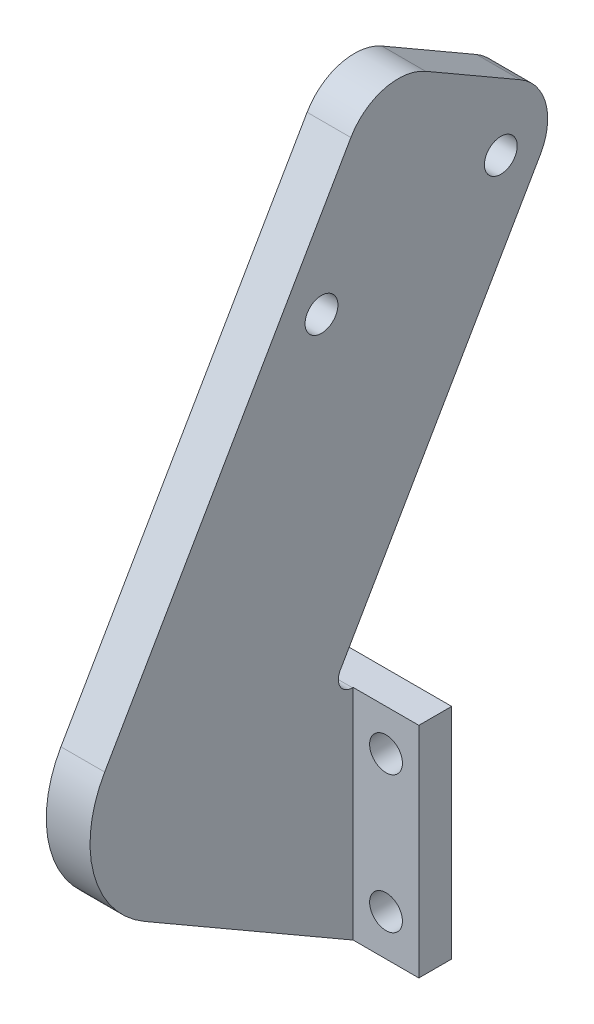
SolidWorks part; units mm, degrees
material "6061-T6 (SS)"
ref_plane "前视基准面" through (0, 0, 0) normal (0, 0, 1) x (1, 0, 0)
ref_plane "上视基准面" through (0, 0, 0) normal (0, 1, 0) x (1, 0, 0)
ref_plane "右视基准面" through (0, 0, 0) normal (1, 0, 0) x (0, 0, -1)
sketch "草图1" plane through (0, 0, 0) normal (0, 0, 1) x (1, 0, 0)
  line L1 (0, 0) -> (17, 0)
  line L2 (0, 0) -> (0, 20)
  line L3 (0, 20) -> (17, 20)
  line L4 (17, 0) -> (17, 20)
  circle A0 centre (3, 16.25) radius 1.5
  circle A1 centre (14, 16.25) radius 1.5
  circle A2 centre (14, 3.75) radius 1.5
  circle A3 centre (3, 3.75) radius 1.5
  dimension "D3" = 3
  dimension "D4" = 3.75
  dimension "D5" = 3
  dimension "D1" = 17
  dimension "D2" = 20
  dimension "D6" = 2
  dimension "D7" = 2
extrude "凸台-拉伸1" add sketch "草图1" along normal blind 3
ref_plane "基准面4" through (6, 0, 0) normal (-1, 0, 0) x (0, 0, 1)
sketch "草图3" plane through (6, 0, 0) normal (-1, 0, 0) x (0, 0, 1)
  line L0 (3, 20) -> (5.3094, 20)
  line L2 (0.7128, 67.9615) -> (30.7128, 16)
  line L3 (30.7128, 16) -> (3, 0)
  line L5 (3, 0) -> (0, 0) construction
  line L6 (3, 20) -> (3, 0) construction
  line L7 (3, 20) -> (3, 0)
  line L8 (5.3094, 20) -> (-16.6077, 57.9615)
  line L9 (-16.6077, 57.9615) -> (0.7128, 67.9615)
  dimension "D1" = 20
  dimension "D2" = 60
  dimension "D3" = 32
  dimension "D5" = 30
extrude "凸台-拉伸2" add sketch "草图3" against normal blind 5
sketch "草图4" plane through (11, 0, 0) normal (1, 0, 0) x (0, 0, -1)
  line L1 (-30.7128, 16) -> (-0.7128, 67.9615) construction
  line L3 (-0.7128, 67.9615) -> (16.6077, 57.9615) construction
  circle A0 centre (-5.8987, 50.9793) radius 1.5
  circle A1 centre (10.4936, 55.3716) radius 1.5
  dimension "D1" = 5.3
  dimension "D2" = 3
  dimension "D3" = 4
  dimension "D4" = 3
  dimension "D5" = 16.3923
  dimension "D6" = 16
extrude "切除-拉伸1" cut sketch "草图4" against normal blind 5
fillet "圆角2" radius 5 2 edges at (8.5, 67.9615, 0.7128) (8.5, 57.9615, -16.6077)
fillet "圆角3" radius 1.3 1 edges at (8.5, 20, 5.3094)
fillet "圆角4" radius 10 1 edges at (8.5, 16, 30.7128)
sketch "草图5" plane through (0, 0, 3) normal (0, 0, 1) x (1, 0, 0)
  line L1 (0, 20) -> (6, 20)
  line L2 (0, 20) -> (0, 0)
  line L3 (0, 0) -> (6, 0)
  line L4 (6, 20) -> (6, 0)
extrude "切除-拉伸2" cut sketch "草图5" against normal blind 10
sketch "草图6" plane through (6, 0, 0) normal (-1, 0, 0) x (0, 0, 1)
  line L7 (3, 0) -> (22.0526, 11)
  line L8 (25.7128, 24.6603) -> (3.2128, 63.6314)
  line L9 (-3.6173, 65.4615) -> (-12.2776, 60.4615)
  line L10 (-14.1077, 53.6314) -> (4.1836, 21.95)
  line L11 (3.0577, 20) -> (0, 20)
  line L12 (0, 20) -> (0, 0)
  line L13 (0, 0) -> (3, 0)
  line L14 (3, 0) -> (22.0526, 11)
  line L15 (25.7128, 24.6603) -> (3.2128, 63.6314)
  line L16 (-3.6173, 65.4615) -> (-12.2776, 60.4615)
  line L17 (-14.1077, 53.6314) -> (4.1836, 21.95)
  line L18 (3.0577, 20) -> (0, 20)
  line L19 (0, 20) -> (0, 0)
  line L20 (0, 0) -> (3, 0)
  circle A0 centre (5.8987, 50.9793) radius 1.5 construction
  circle A1 centre (-10.4936, 55.3716) radius 1.5 construction
  circle A2 centre (5.8987, 50.9793) radius 1.5
  circle A3 centre (-10.4936, 55.3716) radius 1.5
  arc A4 (22.0526, 11) -> (25.7128, 24.6603) centre (17.0526, 19.6603) ccw
  arc A5 (3.2128, 63.6314) -> (-3.6173, 65.4615) centre (-1.1173, 61.1314) ccw
  arc A6 (-12.2776, 60.4615) -> (-14.1077, 53.6314) centre (-9.7776, 56.1314) ccw
  arc A7 (3.0577, 20) -> (4.1836, 21.95) centre (3.0577, 21.3) ccw
  arc A8 (22.0526, 11) -> (25.7128, 24.6603) centre (17.0526, 19.6603) ccw
  arc A9 (3.2128, 63.6314) -> (-3.6173, 65.4615) centre (-1.1173, 61.1314) ccw
  arc A10 (-12.2776, 60.4615) -> (-14.1077, 53.6314) centre (-9.7776, 56.1314) ccw
  arc A11 (3.0577, 20) -> (4.1836, 21.95) centre (3.0577, 21.3) ccw
  dimension "D1" = 0
extrude "切除-拉伸3" cut sketch "草图6" against normal blind 1
